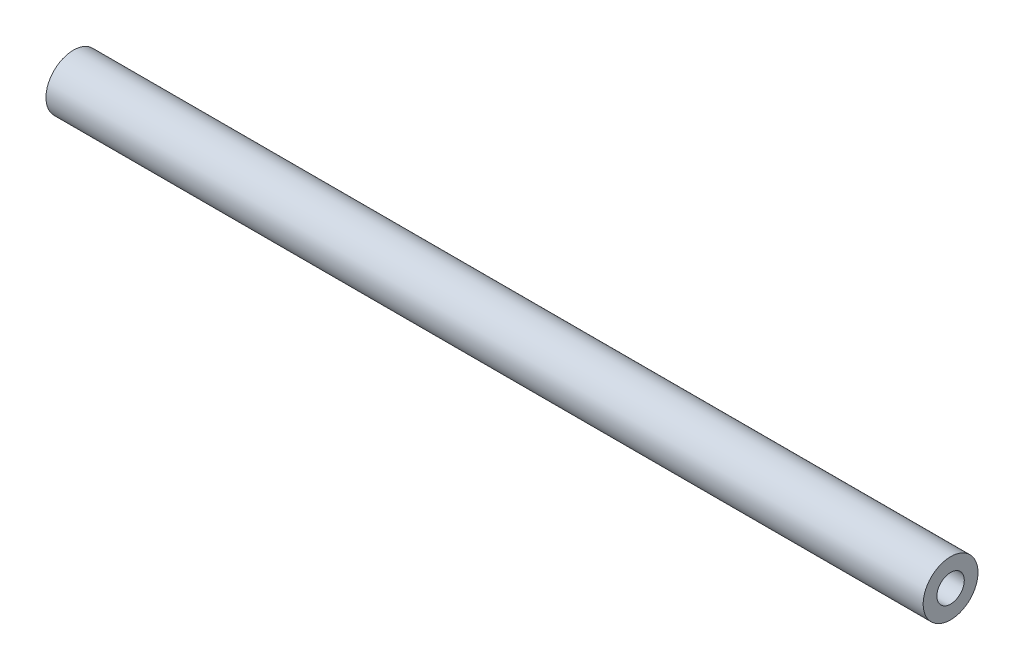
SolidWorks part; units mm, degrees
ref_plane "Front Plane" through (0, 0, 0) normal (0, 0, 1) x (1, 0, 0)
ref_plane "Top Plane" through (0, 0, 0) normal (0, 1, 0) x (1, 0, 0)
ref_plane "Right Plane" through (0, 0, 0) normal (1, 0, 0) x (0, 0, -1)
sketch "Sketch1" plane through (0, 0, 0) normal (1, 0, 0) x (0, 0, -1)
  circle A0 centre (0, 0) radius 3.175
  circle A1 centre (0, 0) radius 6.35
  dimension "D1" = 6.35
  dimension "D2" = 12.7
extrude "Boss-Extrude1" add sketch "Sketch1" along normal blind 203.2
